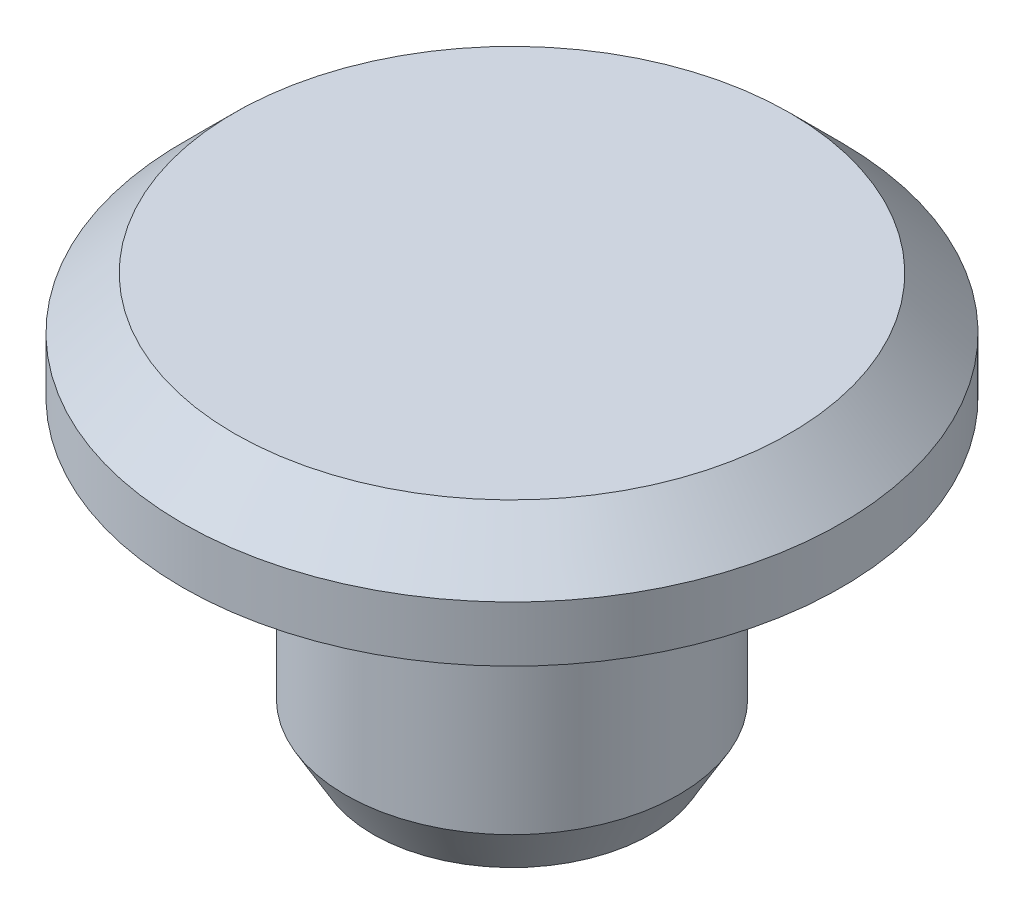
SolidWorks part; units mm, degrees
ref_plane "Front Plane" through (0, 0, 0) normal (0, 0, 1) x (1, 0, 0)
ref_plane "Top Plane" through (0, 0, 0) normal (0, 1, 0) x (1, 0, 0)
ref_plane "Right Plane" through (0, 0, 0) normal (1, 0, 0) x (0, 0, -1)
sketch "Sketch1" plane through (0, 0, 0) normal (0, 0, 1) x (1, 0, 0)
  line L0 (0, 0) -> (0, 7.5)
  line L1 (0, 7.5) -> (-5, 7.5)
  line L3 (-3, 4.5) -> (-3, 0)
  line L4 (-3, 0) -> (0, 0)
  line L5 (-5, 7.5) -> (-5.9326, 6.5674)
  line L7 (0, 14) -> (0, 10.0662) construction
  line L8 (-5.9326, 6.5674) -> (-5.9326, 5.5674)
  line L9 (-5.9326, 5.5674) -> (-3, 4.5)
  point P13 (0, 5.5)
  dimension "D1" = 70
  dimension "D2" = 6
  dimension "D3" = 45
  dimension "D4" = 3
  dimension "D5" = 5.5
  dimension "D6" = 5
  dimension "D7" = 7.5
  dimension "D8" = 1
revolve "Revolve1" add sketch "Sketch1" angle 360 about L7
sketch "Sketch2" plane through (0, 0, 0) normal (0, -1, 0) x (1, 0, 0)
  line L0 (1.75, -1.4142) -> (1.75, 1.4142)
  line L1 (-1.75, 1.4142) -> (-1.75, -1.4142)
  arc A0 (-1.75, 1.4142) -> (1.75, 1.4142) centre (0, 0) cw
  arc A1 (-1.75, -1.4142) -> (1.75, -1.4142) centre (0, 0) ccw
  dimension "D2" = 2.25
  dimension "D1" = 3.5
extrude "Cut-Extrude1" cut sketch "Sketch2" against normal up to vertex (5.5 mm away) up to point (0, 5.5, 0)
chamfer "Chamfer1" distance 0.5 angle 60 1 edges at (0, 0, 3)
